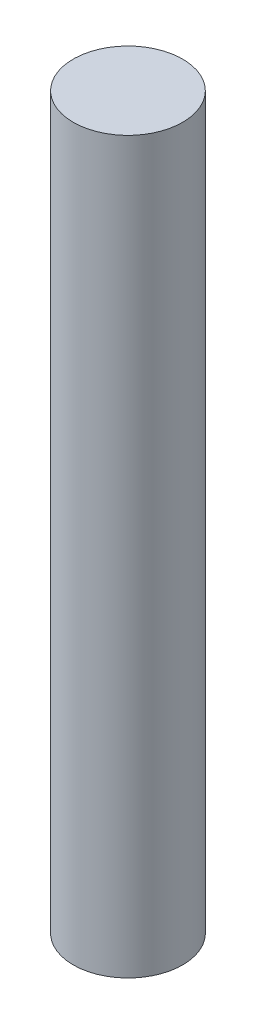
SolidWorks part; units mm, degrees
ref_plane "Front Plane" through (0, 0, 0) normal (0, 0, 1) x (1, 0, 0)
ref_plane "Top Plane" through (0, 0, 0) normal (0, 1, 0) x (1, 0, 0)
ref_plane "Right Plane" through (0, 0, 0) normal (1, 0, 0) x (0, 0, -1)
sketch "Sketch1" plane through (0, 0, 0) normal (0, 1, 0) x (1, 0, 0)
  circle A0 centre (0, 0) radius 1.5
  dimension "D1" = 3
extrude "Boss-Extrude1" add sketch "Sketch1" along normal blind 20
